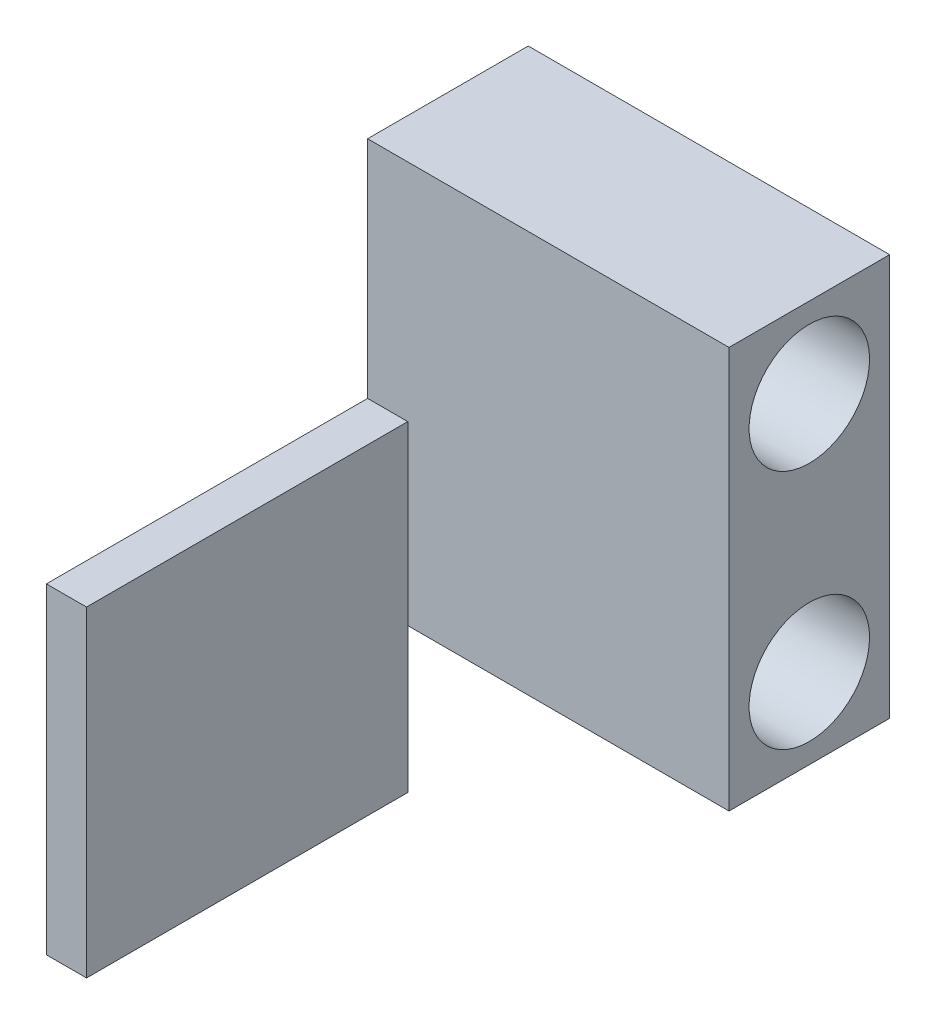
SolidWorks part; units mm, degrees
ref_plane "Front Plane" through (0, 0, 0) normal (0, 0, 1) x (1, 0, 0)
ref_plane "Top Plane" through (0, 0, 0) normal (0, 1, 0) x (1, 0, 0)
ref_plane "Right Plane" through (0, 0, 0) normal (1, 0, 0) x (0, 0, -1)
sketch "Layout Sketch" plane through (0, 0, 0) normal (1, 0, 0) x (0, 0, -1)
  line L0 (0, 15) -> (0, -15) construction
  line L1 (-9.525, 3.4288) -> (9.525, 3.4288) construction
  line L4 (-50, -3) -> (-10, -3)
  line L5 (-50, -3) -> (-50, -43)
  line L6 (-50, -43) -> (-10, -43)
  line L7 (-10, -3) -> (-10, -43)
  line L8 (-50, -3) -> (-10, -43) construction
  line L9 (-50, -43) -> (-10, -3) construction
  line L16 (10, -25) -> (-10, -25)
  line L17 (10, -25) -> (10, 25)
  line L18 (10, 25) -> (-10, 25)
  line L19 (-10, -25) -> (-10, 25)
  line L20 (0, 25) -> (0, -25) construction
  line L21 (10, 0) -> (-10, 0) construction
  circle A0 centre (0, -15) radius 7.5 construction
  circle A1 centre (0, 15) radius 7.5 construction
  circle A2 centre (9.525, 3.4288) radius 1.25
  circle A3 centre (-9.525, 3.4288) radius 1.25
  point P4 (0, 0)
  point P12 (18.6447, 1.6795)
  point P13 (0, 3.4288)
  point P17 (-30, -23)
  point P18 (0, 0)
  point P21 (10.6623, -1.8798)
  point P25 (0, 3.4288)
  point P27 (0, 0)
  dimension "D2" = 15
  dimension "D3" = 15
  dimension "D4" = 2.5
  dimension "D14" = 20
  dimension "D15" = 10
  dimension "D1" = 30
  dimension "D5" = 19.05
  dimension "D6" = 40
  dimension "D7" = 40
  dimension "D8" = 38
  dimension "D12" = 30
sketch "Sketch2" plane through (0, 0, 0) normal (1, 0, 0) x (0, 0, -1)
  line L1 (-10, 25) -> (10, 25)
  line L2 (-10, 25) -> (-10, -25)
  line L3 (-10, -25) -> (10, -25)
  line L4 (10, 25) -> (10, -25)
  line L5 (-10, 25) -> (10, -25) construction
  line L6 (-10, -25) -> (10, 25) construction
  point P4 (0, 0)
extrude "Boss-Extrude1" add sketch "Sketch2" along normal mid plane 45
sketch "Sketch3" plane through (0, 0, 10) normal (0, 0, 1) x (1, 0, 0)
  line L0 (-22.5, 25) -> (-22.5, -25) construction
  line L1 (-22.5, -3) -> (-17.5, -3)
  line L2 (-22.5, -3) -> (-22.5, -43)
  line L3 (-22.5, -43) -> (-17.5, -43)
  line L4 (-17.5, -3) -> (-17.5, -43)
  line L5 (-22.5, -3) -> (-17.5, -43) construction
  line L6 (-22.5, -43) -> (-17.5, -3) construction
  line L7 (-17.5, -3) -> (0, -3) construction
  point P4 (-20, -23)
  dimension "D1" = 40
  dimension "D2" = 5
extrude "Boss-Extrude2" add sketch "Sketch3" along normal blind 40
sketch "Sketch4" plane through (0, 0, 0) normal (1, 0, 0) x (0, 0, -1)
  circle A0 centre (0, -15) radius 7.5 construction
  circle A1 centre (0, 15) radius 7.5 construction
  circle A2 centre (0, -15) radius 7.5
  circle A3 centre (0, 15) radius 7.5
extrude "Cut-Extrude1" cut sketch "Sketch4" against normal through all both and the other way through all
